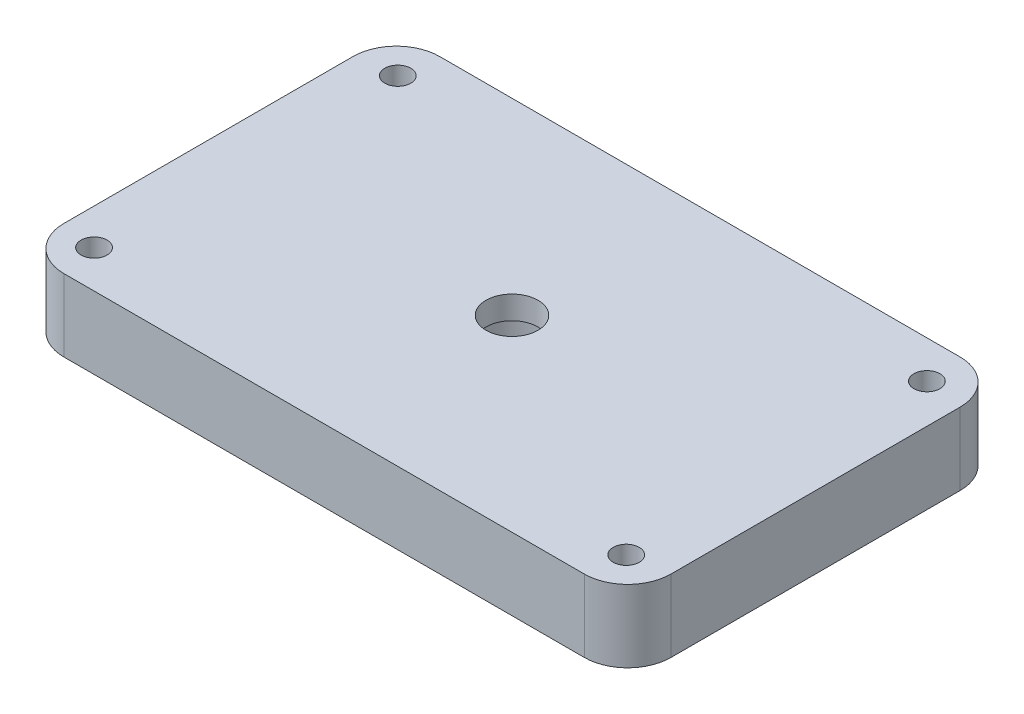
SolidWorks part; units mm, degrees
ref_plane "Front Plane" through (0, 0, 0) normal (0, 0, 1) x (1, 0, 0)
ref_plane "Top Plane" through (0, 0, 0) normal (0, 1, 0) x (1, 0, 0)
ref_plane "Right Plane" through (0, 0, 0) normal (1, 0, 0) x (0, 0, -1)
sketch "Sketch1" plane through (0, 0, 0) normal (0, 1, 0) x (1, 0, 0)
  line L0 (-20.8014, 12.877) -> (26.67, -16.51) construction
  line L1 (-22.86, 16.51) -> (22.86, 16.51)
  line L2 (-26.67, 12.7) -> (-26.67, -12.7)
  line L3 (-22.86, -16.51) -> (-18.7325, -16.51)
  line L4 (26.67, 12.7) -> (26.67, -12.7)
  line L5 (-26.67, 16.51) -> (-22.7451, 14.0803) construction
  line L6 (-26.67, -16.51) -> (26.67, 16.51) construction
  line L7 (18.7325, -16.51) -> (22.86, -16.51)
  line L8 (-18.7325, -16.51) -> (18.7325, -16.51)
  circle A0 centre (-23.241, 13.208) radius 1.143
  circle A1 centre (23.241, 13.208) radius 1.143
  circle A2 centre (23.241, -13.208) radius 1.143
  circle A3 centre (-23.5075, -13.208) radius 1.143
  arc A4 (-22.86, 16.51) -> (-26.67, 12.7) centre (-22.86, 12.7) ccw
  arc A5 (-26.67, -12.7) -> (-22.86, -16.51) centre (-22.86, -12.7) ccw
  arc A6 (22.86, -16.51) -> (26.67, -12.7) centre (22.86, -12.7) ccw
  arc A7 (22.86, 16.51) -> (26.67, 12.7) centre (22.86, 12.7) cw
  point P0 (0, 0)
  point P14 (-24.384, 13.208)
  point P18 (24.384, 14.35)
  dimension "D3" = 2.286
  dimension "D5" = 46.482
  dimension "D7" = 26.416
  dimension "D8" = 13.208
  dimension "D9" = 3.81
  dimension "D1" = 53.34
  dimension "D2" = 33.02
  dimension "D4" = 48.768
  dimension "D6" = 23.241
extrude "Boss-Extrude1" add sketch "Sketch1" along normal blind 6.35
sketch "Sketch2" plane through (0, 0, 0) normal (0, -1, 0) x (1, 0, 0)
  circle A0 centre (0, 0) radius 3.81
  dimension "D1" = 7.62
extrude "Cut-Extrude1" cut sketch "Sketch2" against normal blind 4.318
sketch "Sketch3" plane through (0, 4.318, 0) normal (0, -1, 0) x (-1, 0, 0)
  circle A0 centre (0, 0) radius 2.286
  dimension "D1" = 4.572
extrude "Cut-Extrude2" cut sketch "Sketch3" against normal blind 4.318
